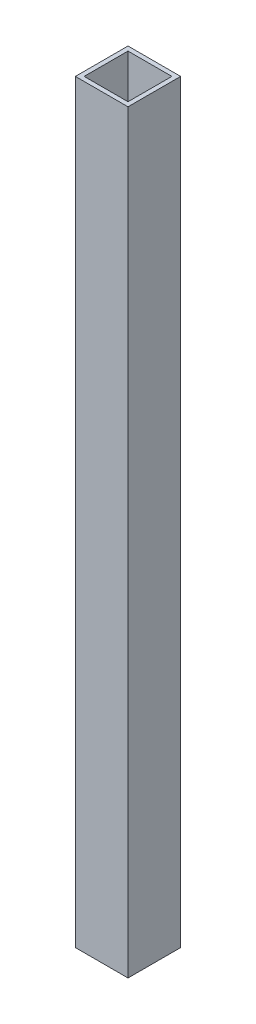
SolidWorks part; units mm, degrees
material "6063-T6"
ref_plane "Front Plane" through (0, 0, 0) normal (0, 0, 1) x (1, 0, 0)
ref_plane "Top Plane" through (0, 0, 0) normal (0, 1, 0) x (1, 0, 0)
ref_plane "Right Plane" through (0, 0, 0) normal (1, 0, 0) x (0, 0, -1)
sketch "Sketch1" plane through (0, 0, 0) normal (0, 1, 0) x (1, 0, 0)
  line L0 (3.175, 34.925) -> (34.925, 34.925)
  line L1 (0, 0) -> (38.1, 0)
  line L2 (0, 0) -> (0, 38.1)
  line L3 (0, 38.1) -> (38.1, 38.1)
  line L4 (38.1, 0) -> (38.1, 38.1)
  line L5 (34.925, 3.175) -> (34.925, 34.925)
  line L6 (3.175, 3.175) -> (34.925, 3.175)
  line L7 (3.175, 3.175) -> (3.175, 34.925)
  dimension "D1" = 38.1
  dimension "D2" = 3.175
extrude "Boss-Extrude1" add sketch "Sketch1" along normal blind 546.1
